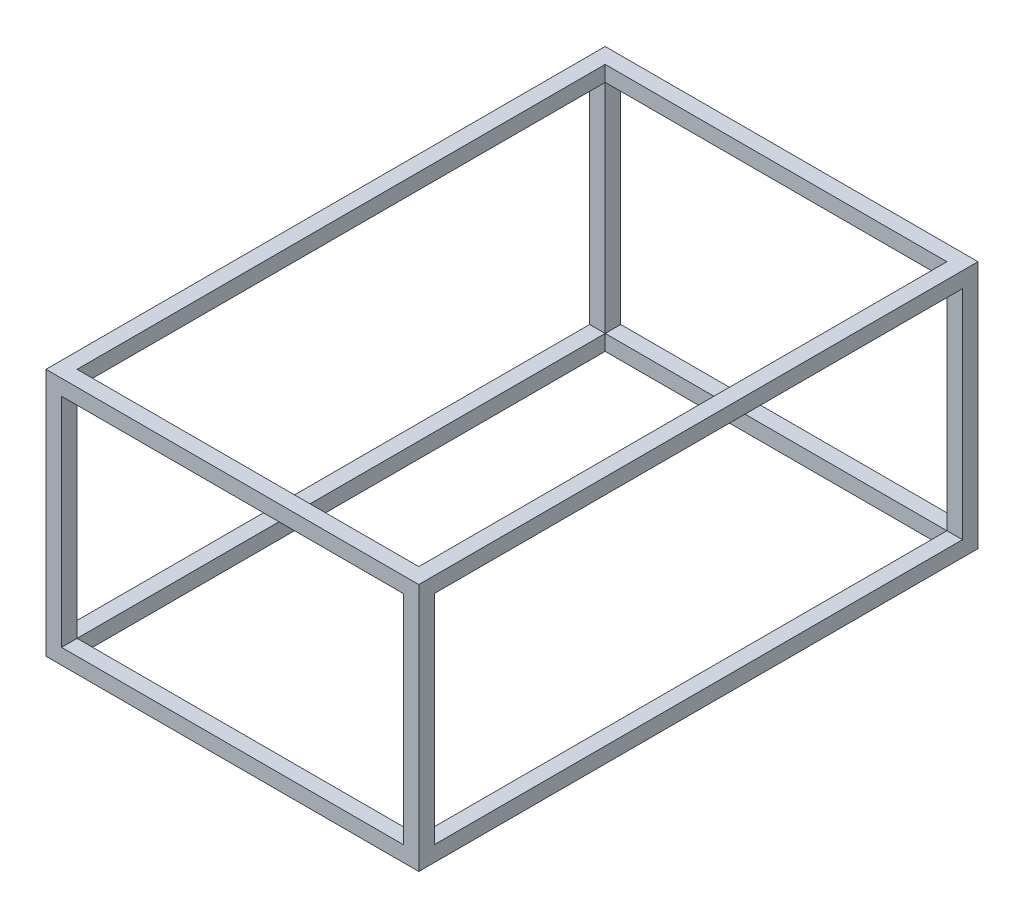
SolidWorks part; units mm, degrees
ref_plane "Front Plane" through (0, 0, 0) normal (0, 0, 1) x (1, 0, 0)
ref_plane "Top Plane" through (0, 0, 0) normal (0, 1, 0) x (1, 0, 0)
ref_plane "Right Plane" through (0, 0, 0) normal (1, 0, 0) x (0, 0, -1)
sketch "Sketch1" plane through (0, 0, 0) normal (0, 1, 0) x (0, 0, -1)
  line L0 (25.4, 25.4) -> (25.4, 584.2)
  line L1 (0, 0) -> (914.4, 0)
  line L2 (0, 0) -> (0, 609.6)
  line L3 (0, 609.6) -> (914.4, 609.6)
  line L4 (914.4, 0) -> (914.4, 609.6)
  line L5 (25.4, 584.2) -> (889, 584.2)
  line L6 (889, 25.4) -> (889, 584.2)
  line L7 (25.4, 25.4) -> (889, 25.4)
  dimension "D1" = 914.4
  dimension "D2" = 609.6
  dimension "D3" = 25.4
extrude "Boss-Extrude1" add sketch "Sketch1" along normal mid plane 25.4
sketch "Sketch2" plane through (0, 12.7, 0) normal (0, 1, 0) x (0, 0, -1)
  line L1 (25.4, 584.2) -> (0, 584.2)
  line L2 (25.4, 584.2) -> (25.4, 609.6)
  line L3 (25.4, 609.6) -> (0, 609.6)
  line L4 (0, 584.2) -> (0, 609.6)
  line L5 (889, 584.2) -> (914.4, 584.2)
  line L6 (889, 584.2) -> (889, 609.6)
  line L7 (889, 609.6) -> (914.4, 609.6)
  line L8 (914.4, 584.2) -> (914.4, 609.6)
  line L9 (889, 25.4) -> (914.4, 25.4)
  line L10 (889, 25.4) -> (889, 0)
  line L11 (889, 0) -> (914.4, 0)
  line L12 (914.4, 25.4) -> (914.4, 0)
  line L13 (0, 0) -> (25.4, 0)
  line L14 (0, 0) -> (0, 25.4)
  line L15 (0, 25.4) -> (25.4, 25.4)
  line L16 (25.4, 0) -> (25.4, 25.4)
extrude "Boss-Extrude2" add sketch "Sketch2" along normal blind 381
sketch "Sketch3" plane through (0, 393.7, 0) normal (0, 1, 0) x (0, 0, -1)
  line L1 (914.4, 0) -> (0, 0)
  line L2 (914.4, 0) -> (914.4, 609.6)
  line L3 (914.4, 609.6) -> (0, 609.6)
  line L4 (0, 0) -> (0, 609.6)
  line L5 (25.4, 584.2) -> (889, 584.2)
  line L6 (25.4, 584.2) -> (25.4, 25.4)
  line L7 (25.4, 25.4) -> (889, 25.4)
  line L8 (889, 584.2) -> (889, 25.4)
extrude "Boss-Extrude3" add sketch "Sketch3" against normal blind 25.4
